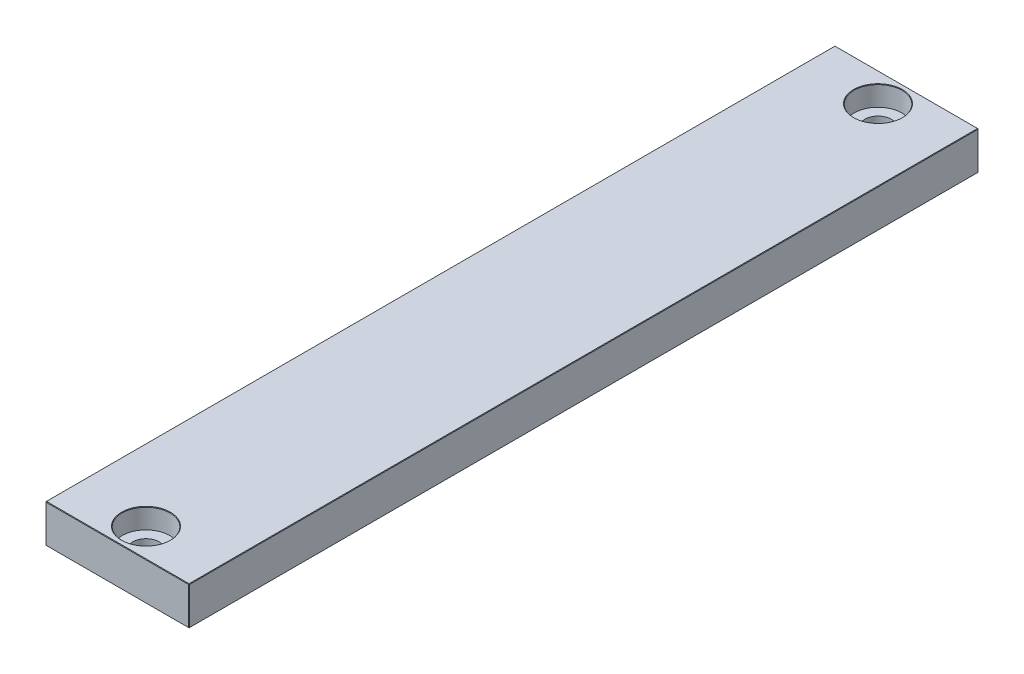
SolidWorks part; units mm, degrees
ref_plane "Front Plane" through (0, 0, 0) normal (0, 0, 1) x (1, 0, 0)
ref_plane "Top Plane" through (0, 0, 0) normal (0, 1, 0) x (1, 0, 0)
ref_plane "Right Plane" through (0, 0, 0) normal (1, 0, 0) x (0, 0, -1)
sketch "Sketch1" plane through (0, 0, 0) normal (0, 1, 0) x (1, 0, 0)
  line L1 (-15, -82.5) -> (15, -82.5)
  line L2 (-15, -82.5) -> (-15, 82.5)
  line L3 (-15, 82.5) -> (15, 82.5)
  line L4 (15, -82.5) -> (15, 82.5)
  line L5 (-15, -82.5) -> (15, 82.5) construction
  line L6 (-15, 82.5) -> (15, -82.5) construction
  circle A0 centre (0, 76.5) radius 2.75
  circle A1 centre (0, -76.5) radius 2.75
  point P0 (0, 0)
  point P12 (15, 76.355)
  dimension "D3" = 5.5
  dimension "D4" = 159
  dimension "D5" = 15
  dimension "D6" = 6
  dimension "D7" = 15
  dimension "D8" = 5.5
  dimension "D1" = 30
  dimension "D2" = 165
extrude "Boss-Extrude2" add sketch "Sketch1" along normal blind 8
sketch "Sketch3" plane through (0, 8, 0) normal (0, 1, 0) x (1, 0, 0)
  circle A0 centre (0, 76.5) radius 5
  circle A1 centre (0, -76.5) radius 5
extrude "Cut-Extrude1" cut sketch "Sketch3" against normal blind 4.2
chamfer "Chamfer1" distance 0.1 angle 45 16 edges at (0, 0, -73.75) (0, 0, 79.25) (0, 8, 81.5) (0, 8, -71.5) (15, 4, -82.5) (0, 0, -82.5) (-15, 4, -82.5) (15, 0, 0) (-15, 0, 0) (15, 4, 82.5) (0, 0, 82.5) (-15, 4, 82.5) (0, 8, 82.5) (15, 8, 0) (-15, 8, 0) (0, 8, -82.5)
